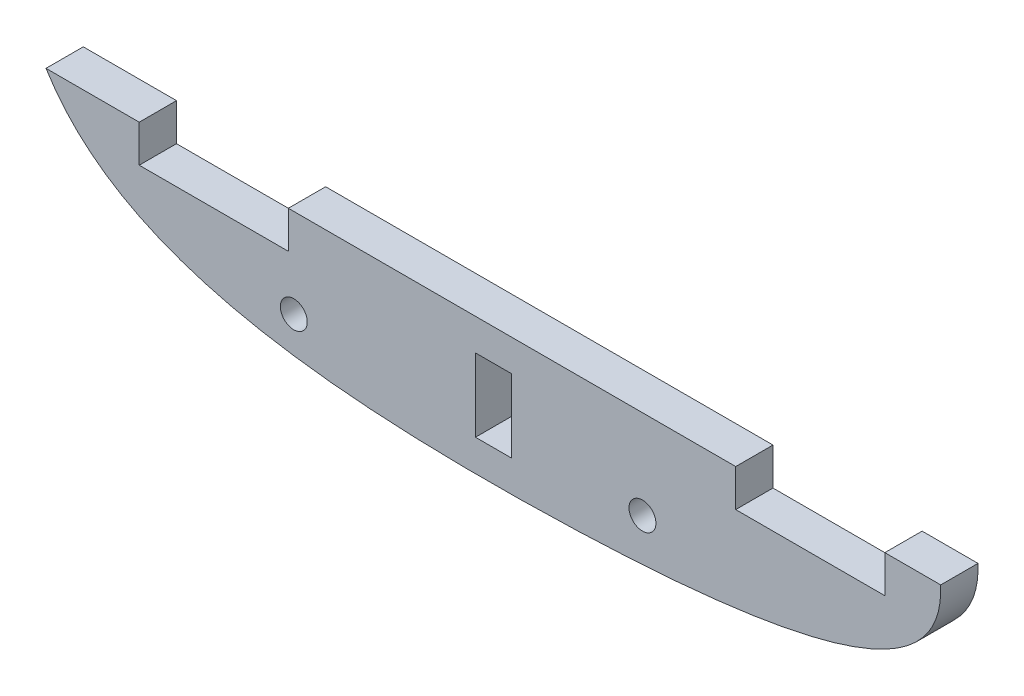
SolidWorks part; units mm, degrees
ref_plane "Front Plane" through (0, 0, 0) normal (0, 0, 1) x (1, 0, 0)
ref_plane "Top Plane" through (0, 0, 0) normal (0, 1, 0) x (1, 0, 0)
ref_plane "Right Plane" through (0, 0, 0) normal (1, 0, 0) x (0, 0, -1)
sketch "Sketch1" plane through (0, 0, 0) normal (0, 0, 1) x (1, 0, 0)
  line L0 (0, 0) -> (152.4, 0) construction
  line L1 (0, 23.2423) -> (15.8806, 23.2423)
  line L2 (76.2, 0) -> (76.2, 23.2423) construction
  line L3 (41.2806, 23.2423) -> (117.4806, 23.2423)
  line L4 (142.8806, 23.2423) -> (152.4, 23.2423)
  line L5 (15.8806, 23.2423) -> (15.8806, 16.8923)
  line L6 (15.8806, 16.8923) -> (41.2806, 16.8923)
  line L7 (41.2806, 23.2423) -> (41.2806, 16.8923)
  line L9 (117.4806, 23.2423) -> (117.4806, 16.8923)
  line L10 (117.4806, 16.8923) -> (142.8806, 16.8923)
  line L11 (142.8806, 23.2423) -> (142.8806, 16.8923)
  line L12 (73.152, 5.3981) -> (79.248, 5.3981)
  line L13 (73.152, 5.3981) -> (73.152, 17.8441)
  line L14 (73.152, 17.8441) -> (79.248, 17.8441)
  line L15 (79.248, 5.3981) -> (79.248, 17.8441)
  line L16 (73.152, 5.3981) -> (79.248, 17.8441) construction
  line L17 (73.152, 17.8441) -> (79.248, 5.3981) construction
  circle A0 centre (101.6, 8.0678) radius 2.2923
  circle A1 centre (42.2078, 8.0678) radius 2.2923
  spline S0 degree 3 poles (0, 23.2423) (9.5957, 7.5717) (37.6916, -0.6233) (137.9245, 0.7351) (152.8213, 10.8513) (152.4, 23.2423) knots 0 0 0 0 0.362369 0.462369 1 1 1 1
  point P5 (76.2, 0)
  point P9 (101.6, 0)
  point P22 (76.2, 11.6211)
  dimension "D2" = 4.5847
  dimension "D3" = 4.5847
  dimension "D1" = 152.4
  dimension "D4" = 6.35
  dimension "D5" = 25.4
  dimension "D6" = 6.35
  dimension "D7" = 25.4
  dimension "D8" = 76.2
  dimension "D9" = 6.096
  dimension "D10" = 12.446
extrude "Boss-Extrude1" add sketch "Sketch1" along normal blind 6.35
